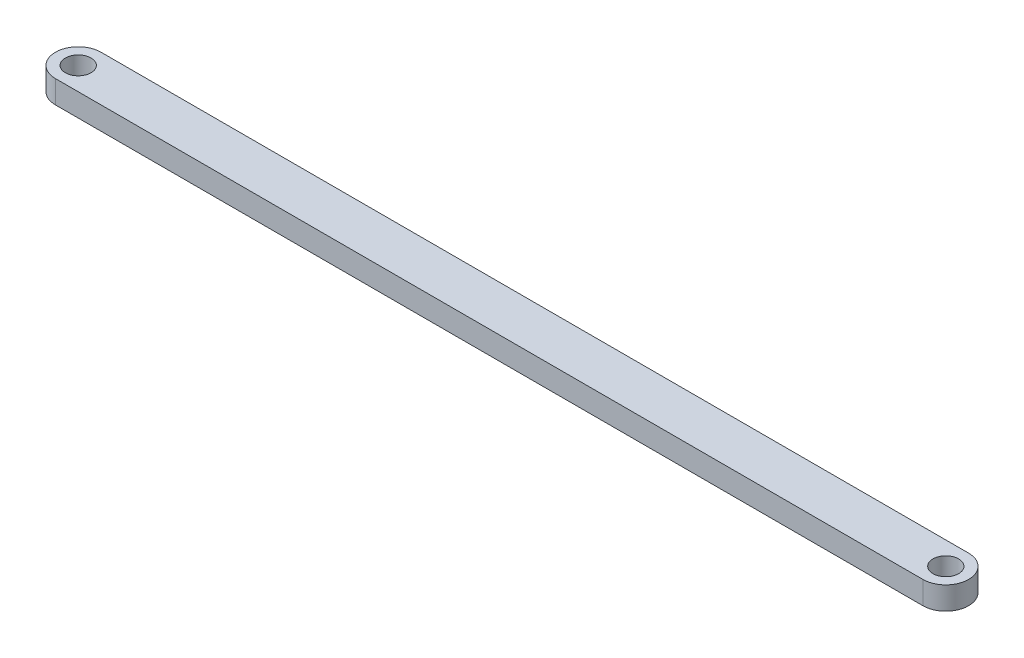
SolidWorks part; units mm, degrees
ref_plane "Front Plane" through (0, 0, 0) normal (0, 0, 1) x (1, 0, 0)
ref_plane "Top Plane" through (0, 0, 0) normal (0, 1, 0) x (1, 0, 0)
ref_plane "Right Plane" through (0, 0, 0) normal (1, 0, 0) x (0, 0, -1)
sketch "Sketch1" plane through (0, 0, 0) normal (0, 1, 0) x (1, 0, 0)
  line L0 (60.3668, 0) -> (-60.3668, 0) construction
  line L1 (60.3668, -3.175) -> (-60.3668, -3.175)
  line L2 (60.3668, 3.175) -> (-60.3668, 3.175)
  arc A0 (60.3668, -3.175) -> (60.3668, 3.175) centre (60.3668, 0) ccw
  arc A1 (-60.3668, 3.175) -> (-60.3668, -3.175) centre (-60.3668, 0) ccw
  point P2 (0, 0)
  dimension "D2" = 3.175
  dimension "D1" = 120.7336
extrude "Boss-Extrude1" add sketch "Sketch1" along normal blind 3.175
hole_wizard "9/64 (0.14063) Diameter Hole1" positions "Sketch3" profile "Sketch2" hole size "9/64" standard "ANSI Inch" end condition through all
sketch "Sketch3" plane through (0, 3.175, 0) normal (0, 1, 0) x (1, 0, 0)
  point P0 (60.3668, 0)
  point P3 (-60.3668, 0)
sketch "Sketch2" plane through (60.3668, 3.175, 0) normal (1, 0, 0) x (0, 0, 1)
  line L0 (0, 0) -> (0, 3.175)
  line L1 (0, 3.175) -> (1.786, 3.175)
  line L2 (1.786, 3.175) -> (1.786, 0)
  line L5 (1.786, 0) -> (0, 0)
  line L11 (0, -6.35) -> (0, 107.95) construction
  dimension "Thru Hole Dia." = 3.572
  dimension "Thru Hole Depth" = 3.175
